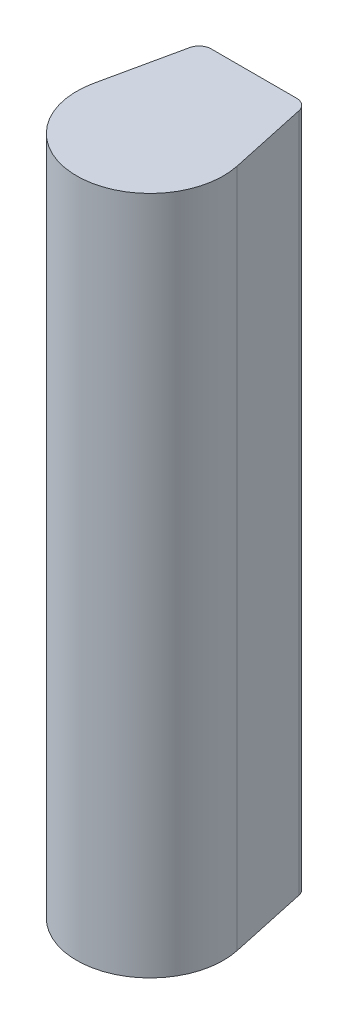
SolidWorks part; units mm, degrees
material "6061-T6 (SS)"
ref_plane "Front Plane" through (0, 0, 0) normal (0, 0, 1) x (1, 0, 0)
ref_plane "Top Plane" through (0, 0, 0) normal (0, 1, 0) x (1, 0, 0)
ref_plane "Right Plane" through (0, 0, 0) normal (1, 0, 0) x (0, 0, -1)
sketch "Sketch5" plane through (0, 0, 0) normal (0, 1, 0) x (1, 0, 0)
  line L0 (-10.922, 21.59) -> (10.922, 21.59)
  line L1 (0, 0) -> (0, 37.164) construction
  line L2 (-14.8954, 3.2223) -> (-10.922, 21.59)
  line L3 (14.8954, 3.2223) -> (10.922, 21.59)
  arc A0 (-14.8954, 3.2223) -> (14.8954, 3.2223) centre (0, 0) ccw
  dimension "D1" = 30.48
  dimension "D2" = 21.59
  dimension "D3" = 21.844
extrude "Extrude1" add sketch "Sketch5" along normal blind 50.8
fillet "Fillet1" radius 2.54 2 edges at (-10.922, 25.4, -21.59) (10.922, 25.4, -21.59)
sketch "Sketch10" plane through (0, 50.8, 0) normal (0, 1, 0) x (1, 0, 0)
  line L3 (8.8727, 21.59) -> (-8.8727, 21.59)
  line L4 (-11.3553, 19.5871) -> (-14.8954, 3.2223)
  line L5 (14.8954, 3.2223) -> (11.3553, 19.5871)
  line L6 (8.8727, 21.59) -> (-8.8727, 21.59)
  line L7 (-11.3553, 19.5871) -> (-14.8954, 3.2223)
  line L8 (14.8954, 3.2223) -> (11.3553, 19.5871)
  arc A3 (-8.8727, 21.59) -> (-11.3553, 19.5871) centre (-8.8727, 19.05) ccw
  arc A4 (-14.8954, 3.2223) -> (14.8954, 3.2223) centre (0, 0) ccw
  arc A5 (11.3553, 19.5871) -> (8.8727, 21.59) centre (8.8727, 19.05) ccw
  arc A6 (-8.8727, 21.59) -> (-11.3553, 19.5871) centre (-8.8727, 19.05) ccw
  arc A7 (-14.8954, 3.2223) -> (14.8954, 3.2223) centre (0, 0) ccw
  arc A8 (11.3553, 19.5871) -> (8.8727, 21.59) centre (8.8727, 19.05) ccw
  dimension "D1" = 0
extrude "Extrude2" add sketch "Sketch10" along normal blind 90.3545
sketch "Sketch11" [suppressed] plane through (0, 50.8, 0) normal (0, 1, 0) x (1, 0, 0)
  line L3 (8.8727, 21.59) -> (-8.8727, 21.59)
  line L4 (-11.3553, 19.5871) -> (-14.8954, 3.2223)
  line L5 (14.8954, 3.2223) -> (11.3553, 19.5871)
  line L6 (8.8727, 21.59) -> (-8.8727, 21.59)
  line L7 (-11.3553, 19.5871) -> (-14.8954, 3.2223)
  line L8 (14.8954, 3.2223) -> (11.3553, 19.5871)
  arc A3 (-8.8727, 21.59) -> (-11.3553, 19.5871) centre (-8.8727, 19.05) ccw
  arc A4 (-14.8954, 3.2223) -> (14.8954, 3.2223) centre (0, 0) ccw
  arc A5 (11.3553, 19.5871) -> (8.8727, 21.59) centre (8.8727, 19.05) ccw
  arc A6 (-8.8727, 21.59) -> (-11.3553, 19.5871) centre (-8.8727, 19.05) ccw
  arc A7 (-14.8954, 3.2223) -> (14.8954, 3.2223) centre (0, 0) ccw
  arc A8 (11.3553, 19.5871) -> (8.8727, 21.59) centre (8.8727, 19.05) ccw
  dimension "D1" = 0
extrude "Extrude3" [suppressed] add sketch "Sketch11" along normal blind 152.4
